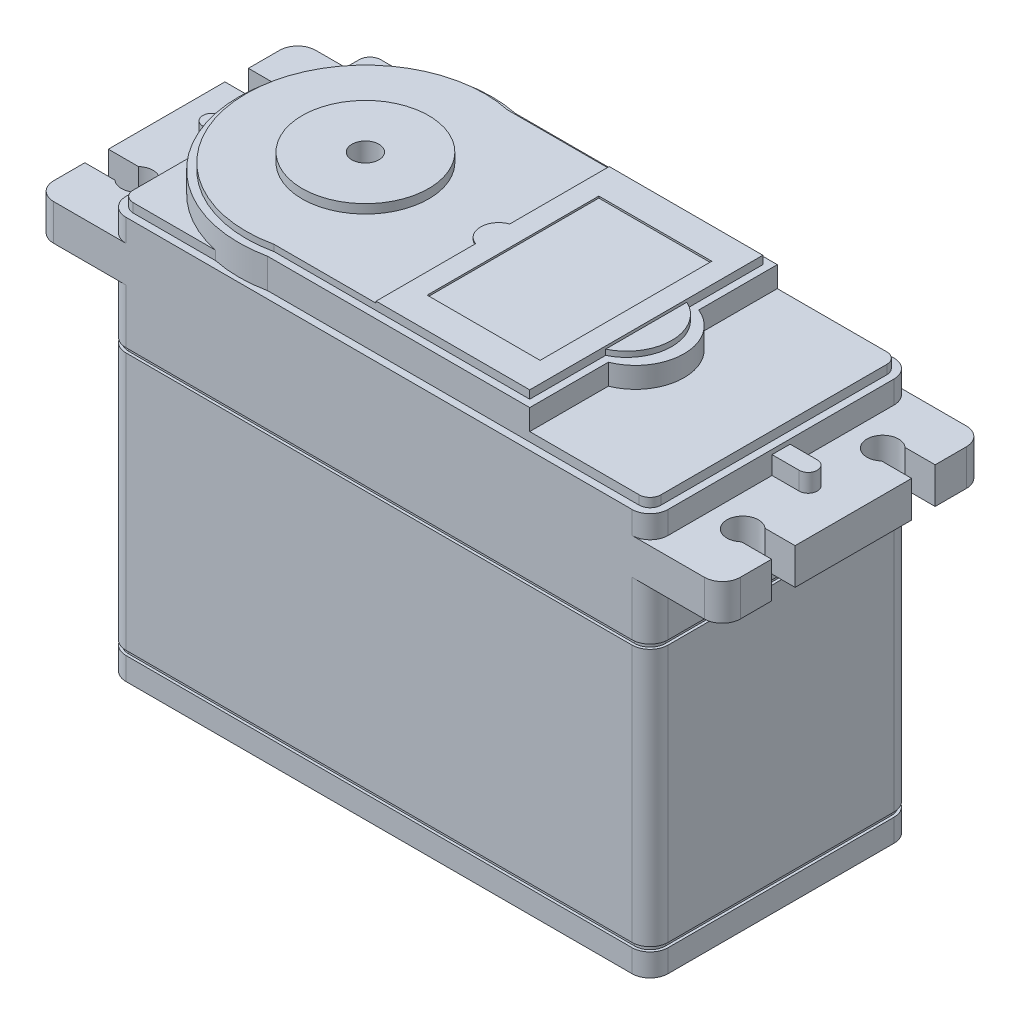
SolidWorks part; units mm, degrees
ref_plane "Front Plane" through (0, 0, 0) normal (0, 0, 1) x (1, 0, 0)
ref_plane "Top Plane" through (0, 0, 0) normal (0, 1, 0) x (1, 0, 0)
ref_plane "Right Plane" through (0, 0, 0) normal (1, 0, 0) x (0, 0, -1)
sketch "Sketch2" plane through (0, 0, 0) normal (0, 1, 0) x (1, 0, 0)
  line L1 (-30, 14.5) -> (30, 14.5)
  line L2 (-30, 14.5) -> (-30, -14.5)
  line L3 (-30, -14.5) -> (30, -14.5)
  line L4 (30, 14.5) -> (30, -14.5)
  line L5 (-30, 14.5) -> (30, -14.5) construction
  line L6 (-30, -14.5) -> (30, 14.5) construction
  point P0 (0, 0)
  dimension "D1" = 60
  dimension "D2" = 29
extrude "Boss-Extrude1" add sketch "Sketch2" along normal blind 46.5
ref_plane "Plane1" through (0, 43, 0) normal (0, 1, 0) x (1, 0, 0)
fillet "Fillet1" radius 2 4 edges at (-30, 23.25, -14.5) (-30, 23.25, 14.5) (30, 23.25, -14.5) (30, 23.25, 14.5)
sketch "Sketch4" plane through (0, 43, 0) normal (0, 1, 0) x (1, 0, 0)
  line L0 (28, 14.5) -> (36, 14.5)
  line L1 (-33.5, 7.75) -> (-38, 7.75) construction
  line L2 (38, 12.5) -> (38, 9.05)
  line L3 (36, -14.5) -> (28, -14.5)
  line L4 (-28, -14.5) -> (28, -14.5) construction
  line L5 (-30, -12.5) -> (-30, 12.5)
  line L6 (30, -12.5) -> (30, 12.5) construction
  line L7 (38, 9.05) -> (34.6715, 9.05)
  line L8 (34.6715, 6.45) -> (38, 6.45)
  line L9 (33.5, 7.75) -> (38, 7.75) construction
  line L10 (38, 6.45) -> (38, -6.45)
  line L11 (-38, 0) -> (38, 0) construction
  line L12 (34.6715, -6.45) -> (38, -6.45)
  line L13 (38, -9.05) -> (34.6715, -9.05)
  line L14 (38, -9.05) -> (38, -12.5)
  line L15 (30, -12.5) -> (30, 12.5)
  line L16 (0, 14.5) -> (0, -14.5) construction
  line L17 (28, 14.5) -> (-28, 14.5) construction
  line L18 (-38, -9.05) -> (-38, -12.5)
  line L19 (-38, -9.05) -> (-34.6715, -9.05)
  line L20 (-34.6715, -6.45) -> (-38, -6.45)
  line L21 (-38, 6.45) -> (-38, -6.45)
  line L22 (-34.6715, 6.45) -> (-38, 6.45)
  line L23 (-38, 9.05) -> (-34.6715, 9.05)
  line L24 (-36, -14.5) -> (-28, -14.5)
  line L25 (-38, 12.5) -> (-38, 9.05)
  line L26 (-28, 14.5) -> (-36, 14.5)
  arc A0 (30, 12.5) -> (28, 14.5) centre (28, 12.5) ccw construction
  arc A1 (36, -14.5) -> (38, -12.5) centre (36, -12.5) ccw
  arc A2 (38, 12.5) -> (36, 14.5) centre (36, 12.5) ccw
  arc A3 (34.6715, 9.05) -> (34.6715, 6.45) centre (33.5, 7.75) ccw
  arc A4 (34.6715, -9.05) -> (34.6715, -6.45) centre (33.5, -7.75) cw
  arc A5 (28, -14.5) -> (30, -12.5) centre (28, -12.5) ccw construction
  arc A6 (30, 12.5) -> (28, 14.5) centre (28, 12.5) ccw
  arc A7 (28, -14.5) -> (30, -12.5) centre (28, -12.5) ccw
  arc A8 (-28, -14.5) -> (-30, -12.5) centre (-28, -12.5) cw
  arc A9 (-30, 12.5) -> (-28, 14.5) centre (-28, 12.5) cw
  arc A10 (-34.6715, -9.05) -> (-34.6715, -6.45) centre (-33.5, -7.75) ccw
  arc A11 (-34.6715, 9.05) -> (-34.6715, 6.45) centre (-33.5, 7.75) cw
  arc A12 (-38, 12.5) -> (-36, 14.5) centre (-36, 12.5) cw
  arc A13 (-36, -14.5) -> (-38, -12.5) centre (-36, -12.5) cw
  point P33 (0, 0)
  dimension "D1" = 2
  dimension "D3" = 3.5
  dimension "D2" = 8
  dimension "D4" = 2.6
  dimension "D5" = 7.75
  dimension "D6" = 3.5
  dimension "D7" = 1.3
extrude "Boss-Extrude2" add sketch "Sketch4" against normal blind 4
sketch "Sketch5" plane through (0, 43, 0) normal (0, 1, 0) x (1, 0, 0)
  line L0 (0, 14.5) -> (0, -14.5) construction
  line L1 (28, 14.5) -> (-28, 14.5) construction
  line L2 (-28, -14.5) -> (28, -14.5) construction
  line L3 (-38, 0) -> (38, 0) construction
  line L4 (-38, 6.45) -> (-38, -6.45) construction
  line L5 (38, -6.45) -> (38, 6.45) construction
  line L6 (30, 1) -> (33, 1)
  line L7 (30, -12.5) -> (30, 12.5) construction
  line L8 (30, -1) -> (33, -1)
  line L9 (30, 1) -> (30, -1)
  line L10 (-30, 1) -> (-30, -1)
  line L11 (-30, -1) -> (-33, -1)
  line L12 (-30, 1) -> (-33, 1)
  arc A0 (33, 1) -> (33, -1) centre (33, 0) cw
  arc A1 (-33, 1) -> (-33, -1) centre (-33, 0) ccw
  dimension "D3" = 3
  dimension "D1" = 2
  dimension "D2" = 1
extrude "Boss-Extrude3" add sketch "Sketch5" along normal blind 2
sketch "Sketch6" plane through (0, 46.5, 0) normal (0, 1, 0) x (1, 0, 0)
  line L4 (28, 14.5) -> (-28, 14.5) construction
  line L5 (-30, 1) -> (-30, 12.5) construction
  line L6 (-30, -12.5) -> (-30, -1) construction
  line L7 (-30, 12.5) -> (-30, -12.5) construction
  line L8 (28, 13.7) -> (-28, 13.7)
  line L9 (-29.2, 12.5) -> (-29.2, -12.5)
  line L10 (-28, -13.7) -> (28, -13.7)
  line L11 (29.2, -12.5) -> (29.2, 12.5)
  line L12 (28, 13.7) -> (-28, 13.7)
  line L13 (-29.2, 12.5) -> (-29.2, -12.5)
  line L14 (-28, -13.7) -> (28, -13.7)
  line L15 (29.2, -12.5) -> (29.2, 12.5)
  line L16 (-28, -14.5) -> (28, -14.5) construction
  line L17 (30, 1) -> (30, -1) construction
  line L18 (30, 12.5) -> (30, 1) construction
  line L19 (30, -12.5) -> (30, 12.5) construction
  line L20 (28, 14.5) -> (-28, 14.5)
  line L21 (-30, 1) -> (-30, 12.5)
  line L22 (-30, -12.5) -> (-30, -1)
  line L23 (-30, 12.5) -> (-30, -12.5)
  line L24 (-28, -14.5) -> (28, -14.5)
  line L25 (30, 1) -> (30, -1)
  line L26 (30, 12.5) -> (30, 1)
  line L27 (30, -12.5) -> (30, 12.5)
  arc A4 (-28, 14.5) -> (-30, 12.5) centre (-28, 12.5) ccw construction
  arc A5 (-30, -12.5) -> (-28, -14.5) centre (-28, -12.5) ccw construction
  arc A6 (28, -14.5) -> (30, -12.5) centre (28, -12.5) ccw construction
  arc A7 (30, 12.5) -> (28, 14.5) centre (28, 12.5) ccw construction
  arc A8 (-28, 13.7) -> (-29.2, 12.5) centre (-28, 12.5) ccw
  arc A9 (-29.2, -12.5) -> (-28, -13.7) centre (-28, -12.5) ccw
  arc A10 (28, -13.7) -> (29.2, -12.5) centre (28, -12.5) ccw
  arc A11 (29.2, 12.5) -> (28, 13.7) centre (28, 12.5) ccw
  arc A12 (-28, 13.7) -> (-29.2, 12.5) centre (-28, 12.5) ccw
  arc A13 (-29.2, -12.5) -> (-28, -13.7) centre (-28, -12.5) ccw
  arc A14 (28, -13.7) -> (29.2, -12.5) centre (28, -12.5) ccw
  arc A15 (29.2, 12.5) -> (28, 13.7) centre (28, 12.5) ccw
  arc A16 (-28, 14.5) -> (-30, 12.5) centre (-28, 12.5) ccw
  arc A17 (-30, -12.5) -> (-28, -14.5) centre (-28, -12.5) ccw
  arc A18 (28, -14.5) -> (30, -12.5) centre (28, -12.5) ccw
  arc A19 (30, 12.5) -> (28, 14.5) centre (28, 12.5) ccw
  line M9 (28, 14.5) -> (-28, 14.5)
  arc M10 (-28, 14.5) -> (-30, 12.5) centre (-28, 12.5) ccw
  line M11 (-30, 12.5) -> (-30, -12.5)
  arc M12 (-30, -12.5) -> (-28, -14.5) centre (-28, -12.5) ccw
  line M13 (-28, -14.5) -> (28, -14.5)
  arc M14 (28, -14.5) -> (30, -12.5) centre (28, -12.5) ccw
  line M15 (30, -12.5) -> (30, 12.5)
  arc M16 (30, 12.5) -> (28, 14.5) centre (28, 12.5) ccw
  dimension "D1" = 0.8
extrude "Cut-Extrude1" cut sketch "Sketch6" against normal blind 1 contours A15 L15 A14 L14 A13 L13 A12 L12 M16 M9 M10 M11 M12 M13 M14 M15
sketch "Sketch7" plane through (0, 46.5, 0) normal (0, 1, 0) x (1, 0, 0)
  line L0 (-38, 0) -> (38, 0) construction
  line L1 (-38, 6.45) -> (-38, -6.45) construction
  line L2 (38, -6.45) -> (38, 6.45) construction
  line L3 (-30, 1) -> (-30, 12.5) construction
  line L4 (15.8827, 13.7) -> (-13.1173, 13.7)
  line L5 (28, 13.7) -> (-28, 13.7) construction
  line L6 (15.8827, 13.7) -> (15.8827, -13.7)
  line L7 (-28, -13.7) -> (28, -13.7) construction
  line L8 (15.8827, -13.7) -> (-13.1173, -13.7)
  line L9 (-28, -13.7) -> (28, -13.7) construction
  line L10 (28, 13.7) -> (-28, 13.7) construction
  arc A0 (-13.1173, 13.7) -> (-13.1173, -13.7) centre (-16, 0) ccw
  dimension "D1" = 14
  dimension "D2" = 28
  dimension "D3" = 29
extrude "Boss-Extrude4" add sketch "Sketch7" along normal blind 3 and the other way up to next
sketch "Sketch8" plane through (0, 49.5, 0) normal (0, 1, 0) x (1, 0, 0)
  line L0 (-13.2018, -12.9) -> (15.0827, -12.9)
  line L1 (15.0827, -12.9) -> (15.0827, 12.9)
  line L2 (15.0827, 12.9) -> (-13.2018, 12.9)
  line L3 (15.8827, -13.7) -> (15.8827, 13.7)
  line L4 (15.8827, 13.7) -> (-13.1173, 13.7)
  line L5 (-13.1173, -13.7) -> (15.8827, -13.7)
  line L6 (15.8827, -13.7) -> (15.8827, 13.7)
  line L7 (15.8827, 13.7) -> (-13.1173, 13.7)
  line L8 (-13.1173, -13.7) -> (15.8827, -13.7)
  arc A0 (-13.2018, 12.9) -> (-13.2018, -12.9) centre (-16, 0) ccw
  arc A1 (-13.1173, 13.7) -> (-13.1173, -13.7) centre (-16, 0) ccw
  arc A2 (-13.1173, 13.7) -> (-13.1173, -13.7) centre (-16, 0) ccw
  dimension "D1" = 0
  dimension "D2" = 0.8
extrude "Cut-Extrude2" cut sketch "Sketch8" against normal blind 0.7
sketch "Sketch9" plane through (0, 48.8, 0) normal (0, 1, 0) x (1, 0, 0)
  line L0 (0, 0) -> (38, 0) construction
  line L1 (38, -6.45) -> (38, 6.45) construction
  line L2 (15.8827, -13.7) -> (15.8827, 13.7) construction
  line L3 (15.8827, 5) -> (15.8827, -5)
  arc A0 (15.8827, 5) -> (15.8827, -5) centre (13.8827, 0) cw
  dimension "D1" = 2
  dimension "D2" = 10
  dimension "D3" = 5
extrude "Boss-Extrude5" add sketch "Sketch9" against normal up to next
sketch "Sketch10" plane through (0, 48.8, 0) normal (0, 1, 0) x (1, 0, 0)
  line L0 (15.0827, -12.9) -> (15.0827, 12.9) construction
  line L1 (15.0827, -12.9) -> (15.0827, 12.9) construction
  line L2 (15.0827, 4.5) -> (15.0827, -4.5)
  arc A3 (15.0827, -4.5) -> (15.0827, 4.5) centre (12.9033, 0) ccw
  dimension "D4" = 5
  dimension "D2" = 9
  dimension "D3" = 4.5
extrude "Boss-Extrude6" add sketch "Sketch10" along normal blind 0.6
ref_plane "Plane2" through (0, 3.5, 0) normal (0, 1, 0) x (1, 0, 0)
sketch "Sketch11" plane through (0, 3.5, 0) normal (0, 1, 0) x (1, 0, 0)
  line L0 (-28, -14.2) -> (28, -14.2)
  line L1 (29.7, -12.5) -> (29.7, 12.5)
  line L2 (28, 14.2) -> (-28, 14.2)
  line L3 (-29.7, 12.5) -> (-29.7, -12.5)
  line L4 (-30, 12.5) -> (-30, -12.5)
  line L5 (28, 14.5) -> (-28, 14.5)
  line L6 (30, -12.5) -> (30, 12.5)
  line L7 (-28, -14.5) -> (28, -14.5)
  line L8 (-30, 12.5) -> (-30, -12.5)
  line L9 (28, 14.5) -> (-28, 14.5)
  line L10 (30, -12.5) -> (30, 12.5)
  line L11 (-28, -14.5) -> (28, -14.5)
  arc A0 (28, -14.2) -> (29.7, -12.5) centre (28, -12.5) ccw
  arc A1 (29.7, 12.5) -> (28, 14.2) centre (28, 12.5) ccw
  arc A2 (-28, 14.2) -> (-29.7, 12.5) centre (-28, 12.5) ccw
  arc A3 (-29.7, -12.5) -> (-28, -14.2) centre (-28, -12.5) ccw
  arc A4 (-28, 14.5) -> (-30, 12.5) centre (-28, 12.5) ccw
  arc A5 (30, 12.5) -> (28, 14.5) centre (28, 12.5) ccw
  arc A6 (28, -14.5) -> (30, -12.5) centre (28, -12.5) ccw
  arc A7 (-30, -12.5) -> (-28, -14.5) centre (-28, -12.5) ccw
  arc A8 (-28, 14.5) -> (-30, 12.5) centre (-28, 12.5) ccw
  arc A9 (30, 12.5) -> (28, 14.5) centre (28, 12.5) ccw
  arc A10 (28, -14.5) -> (30, -12.5) centre (28, -12.5) ccw
  arc A11 (-30, -12.5) -> (-28, -14.5) centre (-28, -12.5) ccw
  dimension "D1" = 0
  dimension "D2" = 0.3
extrude "Cut-Extrude3" cut sketch "Sketch11" along normal blind 0.5
ref_plane "Plane3" through (0, 33, 0) normal (0, 1, 0) x (1, 0, 0)
sketch "Sketch12" plane through (0, 33, 0) normal (0, 1, 0) x (1, 0, 0)
  line L0 (28, 14.2) -> (-28, 14.2)
  line L1 (-29.7, 12.5) -> (-29.7, -12.5)
  line L2 (-28, -14.2) -> (28, -14.2)
  line L3 (29.7, -12.5) -> (29.7, 12.5)
  line L4 (-30, 12.5) -> (-30, -12.5)
  line L5 (28, 14.5) -> (-28, 14.5)
  line L6 (30, -12.5) -> (30, 12.5)
  line L7 (-28, -14.5) -> (28, -14.5)
  line L8 (-30, 12.5) -> (-30, -12.5)
  line L9 (28, 14.5) -> (-28, 14.5)
  line L10 (30, -12.5) -> (30, 12.5)
  line L11 (-28, -14.5) -> (28, -14.5)
  arc A0 (-28, 14.2) -> (-29.7, 12.5) centre (-28, 12.5) ccw
  arc A1 (-29.7, -12.5) -> (-28, -14.2) centre (-28, -12.5) ccw
  arc A2 (28, -14.2) -> (29.7, -12.5) centre (28, -12.5) ccw
  arc A3 (29.7, 12.5) -> (28, 14.2) centre (28, 12.5) ccw
  arc A4 (-30, -12.5) -> (-28, -14.5) centre (-28, -12.5) ccw
  arc A5 (-28, 14.5) -> (-30, 12.5) centre (-28, 12.5) ccw
  arc A6 (30, 12.5) -> (28, 14.5) centre (28, 12.5) ccw
  arc A7 (28, -14.5) -> (30, -12.5) centre (28, -12.5) ccw
  arc A8 (-30, -12.5) -> (-28, -14.5) centre (-28, -12.5) ccw
  arc A9 (-28, 14.5) -> (-30, 12.5) centre (-28, 12.5) ccw
  arc A10 (30, 12.5) -> (28, 14.5) centre (28, 12.5) ccw
  arc A11 (28, -14.5) -> (30, -12.5) centre (28, -12.5) ccw
  dimension "D1" = 0
  dimension "D2" = 0.3
extrude "Cut-Extrude4" cut sketch "Sketch12" against normal blind 0.5
chamfer "Chamfer1" distance 1 angle 45 8 edges at (-30, 0, 0) (30, 0, 0) (0, 0, 14.5) (0, 0, -14.5) (29.4142, 0, 13.9142) (29.4142, 0, -13.9142) (-29.4142, 0, 13.9142) (-29.4142, 0, -13.9142)
sketch "Sketch14" plane through (0, 0, 0) normal (0, -1, 0) x (1, 0, 0)
  line L0 (0, 14.5) -> (0, -14.5) construction
  line L1 (-28, 14.5) -> (28, 14.5) construction
  line L2 (28, -14.5) -> (-28, -14.5) construction
  line L3 (-30, 0) -> (30, 0) construction
  line L4 (-30, 12.5) -> (-30, -12.5) construction
  line L5 (30, -12.5) -> (30, 12.5) construction
  line L6 (-30, 8.1) -> (-25, 8.1)
  line L7 (-30, -12.5) -> (-30, 12.5) construction
  line L8 (-23.6, 9.5) -> (-23.6, 14.5)
  line L9 (30, 8.1) -> (30, 12.5)
  line L10 (-28, 14.5) -> (-23.6, 14.5)
  line L11 (28, 14.5) -> (23.6, 14.5)
  line L12 (-30, 8.1) -> (-30, 12.5)
  line L13 (23.6, 9.5) -> (23.6, 14.5)
  line L14 (30, 8.1) -> (25, 8.1)
  line L15 (30, -8.1) -> (25, -8.1)
  line L16 (23.6, -9.5) -> (23.6, -14.5)
  line L17 (-30, -8.1) -> (-30, -12.5)
  line L18 (28, -14.5) -> (23.6, -14.5)
  line L19 (-28, -14.5) -> (-23.6, -14.5)
  line L20 (30, -8.1) -> (30, -12.5)
  line L21 (-23.6, -9.5) -> (-23.6, -14.5)
  line L22 (-30, -8.1) -> (-25, -8.1)
  arc A0 (-25, 8.1) -> (-23.6, 9.5) centre (-25, 9.5) ccw
  arc A1 (-28, 14.5) -> (-30, 12.5) centre (-28, 12.5) ccw construction
  arc A2 (-28, 14.5) -> (-30, 12.5) centre (-28, 12.5) ccw
  arc A3 (28, 14.5) -> (30, 12.5) centre (28, 12.5) cw
  arc A4 (25, 8.1) -> (23.6, 9.5) centre (25, 9.5) cw
  arc A5 (25, -8.1) -> (23.6, -9.5) centre (25, -9.5) ccw
  arc A6 (28, -14.5) -> (30, -12.5) centre (28, -12.5) ccw
  arc A7 (-28, -14.5) -> (-30, -12.5) centre (-28, -12.5) cw
  arc A8 (-25, -8.1) -> (-23.6, -9.5) centre (-25, -9.5) cw
  dimension "D2" = 1.4
  dimension "D1" = 5
extrude "Cut-Extrude5" cut sketch "Sketch14" against normal blind 1
sketch "Sketch15" plane through (0, 1, 0) normal (0, -1, 0) x (1, 0, 0)
  line L0 (-30, 8.1) -> (-23.6, 14.5) construction
  line L1 (-27.1, 11) -> (-27.1, 9.8)
  line L2 (-27.1, 12.8) -> (-26.5, 12.8)
  line L3 (-27.1, 12.8) -> (-27.1, 11.6)
  line L4 (-27.1, 9.8) -> (-26.5, 9.8)
  line L5 (-26.5, 12.8) -> (-26.5, 11.6)
  line L6 (-27.1, 12.8) -> (-26.5, 9.8) construction
  line L7 (-27.1, 9.8) -> (-26.5, 12.8) construction
  line L8 (-28.3, 11.6) -> (-27.1, 11.6)
  line L9 (-28.3, 11.6) -> (-28.3, 11)
  line L10 (-28.3, 11) -> (-27.1, 11)
  line L11 (-25.3, 11.6) -> (-25.3, 11)
  line L12 (-28.3, 11.6) -> (-25.3, 11) construction
  line L13 (-28.3, 11) -> (-25.3, 11.6) construction
  line L14 (-26.5, 11.6) -> (-25.3, 11.6)
  line L15 (-26.5, 11) -> (-26.5, 9.8)
  line L16 (-26.5, 11) -> (-25.3, 11)
  line L17 (0, 14.5) -> (0, -14.5) construction
  line L18 (-23.6, 14.5) -> (23.6, 14.5) construction
  line L19 (23.6, -14.5) -> (-23.6, -14.5) construction
  line L20 (-30, 0) -> (30, 0) construction
  line L21 (-30, 12.5) -> (-30, -12.5) construction
  line L22 (30, -12.5) -> (30, 12.5) construction
  line L23 (28.3, 11) -> (25.3, 11.6) construction
  line L24 (28.3, 11.6) -> (25.3, 11) construction
  line L25 (27.1, 9.8) -> (26.5, 12.8) construction
  line L26 (27.1, 12.8) -> (26.5, 9.8) construction
  line L27 (30, 8.1) -> (23.6, 14.5) construction
  line L28 (26.5, 11) -> (25.3, 11)
  line L29 (26.5, 11) -> (26.5, 9.8)
  line L30 (26.5, 11.6) -> (25.3, 11.6)
  line L31 (25.3, 11.6) -> (25.3, 11)
  line L32 (28.3, 11) -> (27.1, 11)
  line L33 (28.3, 11.6) -> (28.3, 11)
  line L34 (28.3, 11.6) -> (27.1, 11.6)
  line L35 (26.5, 12.8) -> (26.5, 11.6)
  line L36 (27.1, 9.8) -> (26.5, 9.8)
  line L37 (27.1, 12.8) -> (27.1, 11.6)
  line L38 (27.1, 12.8) -> (26.5, 12.8)
  line L39 (27.1, 11) -> (27.1, 9.8)
  line L40 (30, -8.1) -> (23.6, -14.5) construction
  line L41 (27.1, -12.8) -> (26.5, -9.8) construction
  line L42 (27.1, -9.8) -> (26.5, -12.8) construction
  line L43 (28.3, -11.6) -> (25.3, -11) construction
  line L44 (28.3, -11) -> (25.3, -11.6) construction
  line L45 (-28.3, -11) -> (-25.3, -11.6) construction
  line L46 (-28.3, -11.6) -> (-25.3, -11) construction
  line L47 (-27.1, -9.8) -> (-26.5, -12.8) construction
  line L48 (-27.1, -12.8) -> (-26.5, -9.8) construction
  line L49 (-30, -8.1) -> (-23.6, -14.5) construction
  line L50 (27.1, -11) -> (27.1, -9.8)
  line L51 (27.1, -12.8) -> (26.5, -12.8)
  line L52 (27.1, -12.8) -> (27.1, -11.6)
  line L53 (27.1, -9.8) -> (26.5, -9.8)
  line L54 (26.5, -12.8) -> (26.5, -11.6)
  line L55 (28.3, -11.6) -> (27.1, -11.6)
  line L56 (28.3, -11.6) -> (28.3, -11)
  line L57 (28.3, -11) -> (27.1, -11)
  line L58 (25.3, -11.6) -> (25.3, -11)
  line L59 (26.5, -11.6) -> (25.3, -11.6)
  line L60 (26.5, -11) -> (26.5, -9.8)
  line L61 (26.5, -11) -> (25.3, -11)
  line L62 (-26.5, -11) -> (-25.3, -11)
  line L63 (-26.5, -11) -> (-26.5, -9.8)
  line L64 (-26.5, -11.6) -> (-25.3, -11.6)
  line L65 (-25.3, -11.6) -> (-25.3, -11)
  line L66 (-28.3, -11) -> (-27.1, -11)
  line L67 (-28.3, -11.6) -> (-28.3, -11)
  line L68 (-28.3, -11.6) -> (-27.1, -11.6)
  line L69 (-26.5, -12.8) -> (-26.5, -11.6)
  line L70 (-27.1, -9.8) -> (-26.5, -9.8)
  line L71 (-27.1, -12.8) -> (-27.1, -11.6)
  line L72 (-27.1, -12.8) -> (-26.5, -12.8)
  line L73 (-27.1, -11) -> (-27.1, -9.8)
  circle A0 centre (-26.8, 11.3) radius 2
  circle A1 centre (26.8, 11.3) radius 2
  circle A2 centre (26.8, -11.3) radius 2
  circle A3 centre (-26.8, -11.3) radius 2
  dimension "D1" = 4
  dimension "D2" = 3
  dimension "D3" = 0.6
  dimension "D5" = 3
extrude "Boss-Extrude7" add sketch "Sketch15" along normal blind 0.9
fillet "Fillet2" radius 0.3 4 edges at (-26.8, 0.1, -9.3) (26.8, 0.1, -13.3) (26.8, 0.1, 13.3) (-26.8, 0.1, 9.3)
sketch "Sketch16" plane through (0, 49.5, 0) normal (0, 1, 0) x (1, 0, 0)
  circle A0 centre (-16, 0) radius 7
  dimension "D1" = 14
extrude "Boss-Extrude8" add sketch "Sketch16" along normal blind 1
sketch "Sketch17" plane through (0, 50.5, 0) normal (0, 1, 0) x (1, 0, 0)
  circle A0 centre (-16, 0) radius 1.5
  dimension "D1" = 3
extrude "Cut-Extrude6" cut sketch "Sketch17" against normal blind 10
sketch "Sketch18" plane through (0, 49.5, 0) normal (0, 1, 0) x (1, 0, 0)
  line L0 (-1.9173, 12.9) -> (15.0827, 12.9)
  line L1 (15.0827, 12.9) -> (-13.2018, 12.9) construction
  line L2 (15.0827, 12.9) -> (15.0827, -12.9)
  line L3 (15.0827, -12.9) -> (-1.9173, -12.9)
  line L4 (-13.2018, -12.9) -> (15.0827, -12.9) construction
  line L5 (-1.9173, -12.9) -> (-1.9173, -1.8856)
  line L6 (-16, 0) -> (15.0827, 0) construction
  line L7 (-1.9173, 1.8856) -> (-1.9173, 12.9)
  arc A0 (-1.9173, 1.8856) -> (-1.9173, -1.8856) centre (-1.2507, 0) ccw
  dimension "D2" = 2
  dimension "D1" = 17
  dimension "D3" = 11.9511
extrude "Boss-Extrude9" add sketch "Sketch18" along normal blind 0.2
sketch "Sketch19" plane through (0, 49.7, 0) normal (0, 1, 0) x (1, 0, 0)
  line L0 (15.0827, 12.9) -> (-1.9173, -12.9) construction
  line L2 (0.3327, 9.5) -> (12.8327, 9.5)
  line L3 (0.3327, 9.5) -> (0.3327, -9.5)
  line L4 (0.3327, -9.5) -> (12.8327, -9.5)
  line L5 (12.8327, 9.5) -> (12.8327, -9.5)
  line L6 (0.3327, 9.5) -> (12.8327, -9.5) construction
  line L7 (0.3327, -9.5) -> (12.8327, 9.5) construction
  point P4 (6.5827, 0)
  dimension "D1" = 12.5
  dimension "D2" = 19
extrude "Cut-Extrude7" cut sketch "Sketch19" against normal blind 0.2
sketch "Sketch21" plane through (-30, 0, 0) normal (-1, 0, 0) x (0, 0, 1)
  line L0 (0, 0) -> (0, 32.5) construction
  line L1 (-12.5, 32.5) -> (12.5, 32.5) construction
  line L2 (-12.5, 4) -> (12.5, 4) construction
  line L3 (-3.25, 9.25) -> (3.25, 9.25)
  line L4 (-3.25, 9.25) -> (-3.25, 4.75)
  line L5 (-3.25, 4.75) -> (3.25, 4.75)
  line L6 (3.25, 9.25) -> (3.25, 4.75)
  line L7 (-3.25, 9.25) -> (3.25, 4.75) construction
  line L8 (-3.25, 4.75) -> (3.25, 9.25) construction
  point P5 (0, 7)
  dimension "D1" = 6.5
  dimension "D2" = 4.5
  dimension "D3" = 3
extrude "Boss-Extrude10" add sketch "Sketch21" along normal blind 5.2
sketch "Sketch24" plane through (0, 0, -3.25) normal (0, 0, -1) x (-1, 0, 0)
  line L0 (30, 9.25) -> (35.2, 9.25)
  line L1 (35.2, 9.25) -> (35.2, 8.25)
  line L2 (35.2, 9.25) -> (35.2, 4.75) construction
  line L3 (35.2, 8.25) -> (30, 9.25)
  line L4 (30, 7) -> (35.2, 7) construction
  line L5 (30, 9.25) -> (30, 4.75) construction
  line L6 (35.2, 5.75) -> (30, 4.75)
  line L7 (35.2, 4.75) -> (35.2, 5.75)
  line L8 (30, 4.75) -> (35.2, 4.75)
  dimension "D1" = 1
extrude "Cut-Extrude13" cut sketch "Sketch24" against normal up to next
sketch "Sketch25" plane through (-35.2, 0, 0) normal (-1, 0, 0) x (0, 0, 1)
  line L0 (-3.25, 5.75) -> (3.25, 8.25) construction
  line L1 (3.25, 8.25) -> (-3.25, 8.25) construction
  line L2 (-2.75, 7.75) -> (2.75, 7.75)
  line L3 (-2.75, 7.75) -> (-2.75, 6.25)
  line L4 (-2.75, 6.25) -> (2.75, 6.25)
  line L5 (2.75, 7.75) -> (2.75, 6.25)
  line L6 (-2.75, 7.75) -> (2.75, 6.25) construction
  line L7 (-2.75, 6.25) -> (2.75, 7.75) construction
  line L8 (3.25, 5.75) -> (3.25, 8.25) construction
  line L9 (3.25, 5.75) -> (-3.25, 5.75) construction
  point P4 (0, 7)
  dimension "D1" = 0.5
  dimension "D2" = 0.5
  dimension "D3" = 0.5
extrude "Cut-Extrude14" cut sketch "Sketch25" against normal blind 7.2
